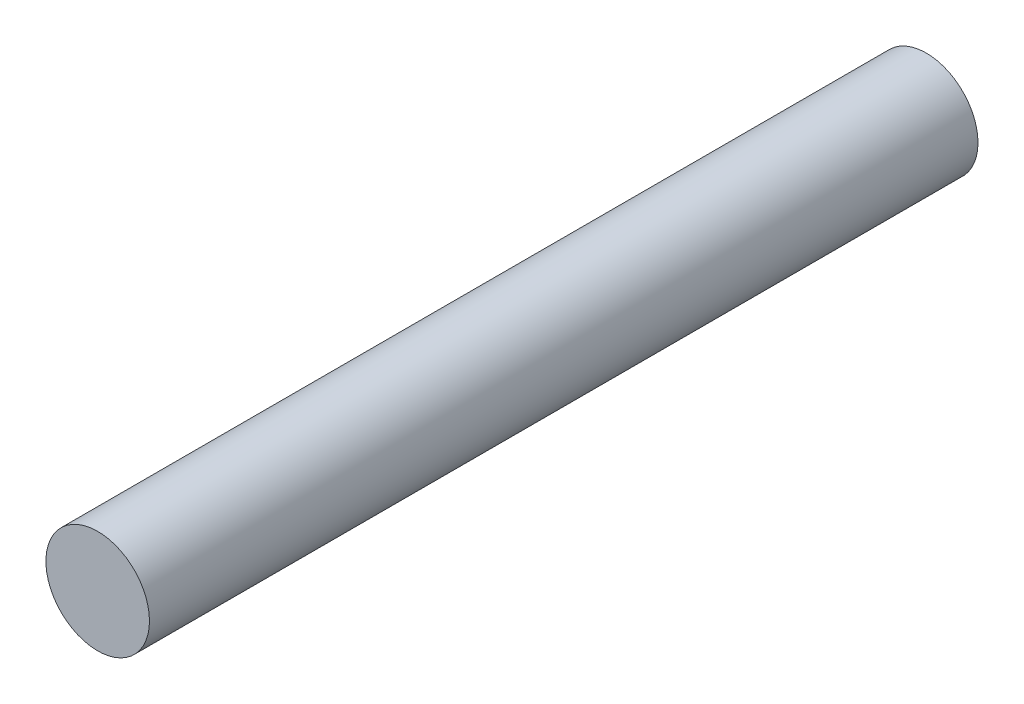
SolidWorks part; units mm, degrees
ref_plane "Front Plane" through (0, 0, 0) normal (0, 0, 1) x (1, 0, 0)
ref_plane "Top Plane" through (0, 0, 0) normal (0, 1, 0) x (1, 0, 0)
ref_plane "Right Plane" through (0, 0, 0) normal (1, 0, 0) x (0, 0, -1)
sketch "Sketch1" plane through (0, 0, 0) normal (0, 1, 0) x (1, 0, 0)
  line L1 (0, 0) -> (3.175, 0)
  line L2 (0, 0) -> (0, 50.8)
  line L3 (0, 50.8) -> (3.175, 50.8)
  line L4 (3.175, 0) -> (3.175, 50.8)
  dimension "D1" = 3.175
  dimension "D2" = 50.8
revolve "Revolve1" add sketch "Sketch1" angle 360 about L2
